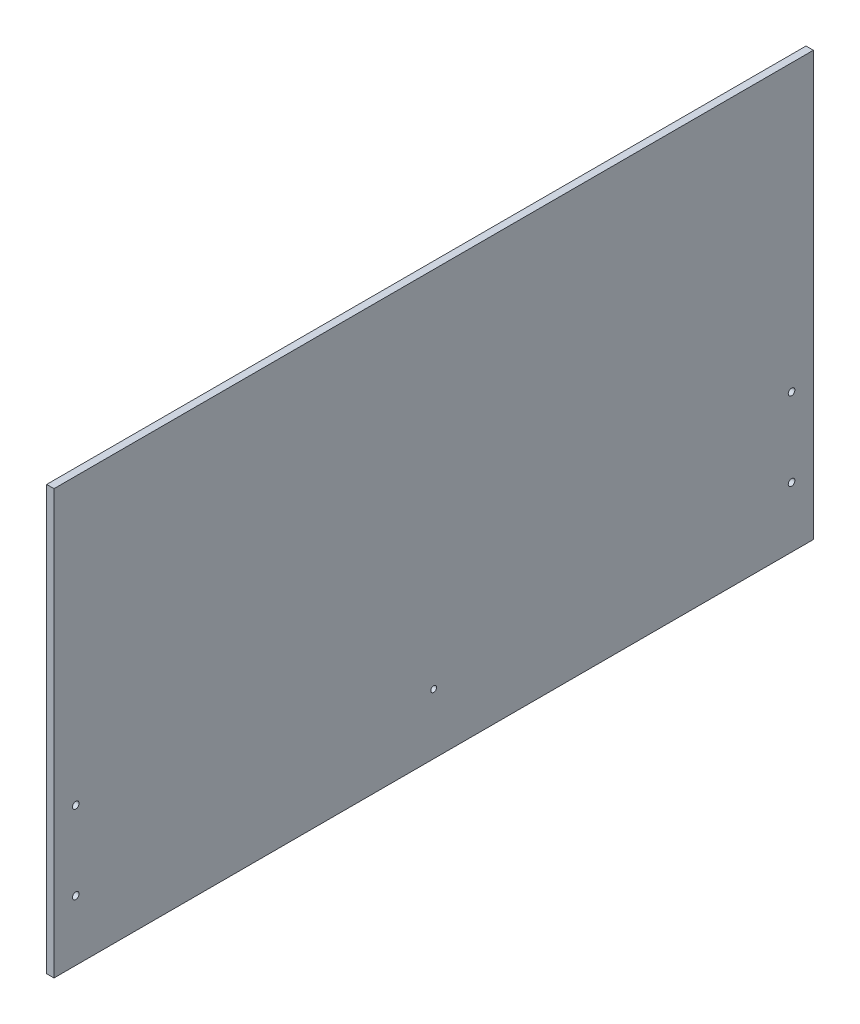
SolidWorks part; units mm, degrees
ref_plane "Front Plane" through (0, 0, 0) normal (0, 0, 1) x (1, 0, 0)
ref_plane "Top Plane" through (0, 0, 0) normal (0, 1, 0) x (1, 0, 0)
ref_plane "Right Plane" through (0, 0, 0) normal (1, 0, 0) x (0, 0, -1)
sketch "Sketch1" plane through (0, 0, 0) normal (1, 0, 0) x (0, 0, -1)
  line L1 (-246.0625, -137.3187) -> (246.0625, -137.3187)
  line L2 (-246.0625, -137.3187) -> (-246.0625, 137.3188)
  line L3 (-246.0625, 137.3188) -> (246.0625, 137.3188)
  line L4 (246.0625, -137.3187) -> (246.0625, 137.3188)
  line L5 (-246.0625, -137.3187) -> (246.0625, 137.3188) construction
  line L6 (-246.0625, 137.3188) -> (246.0625, -137.3187) construction
  point P0 (0, 0)
  dimension "D1" = 274.6375
  dimension "D2" = 492.125
extrude "Boss-Extrude1" add sketch "Sketch1" along normal blind 4.7625
sketch "Sketch2" plane through (4.7625, 0, 0) normal (1, 0, 0) x (0, 0, -1)
  line L0 (0, 0) -> (42.4264, 42.4264) construction
  line L1 (-24.8528, -60) -> (24.8528, -60)
  line L2 (-60, -24.8528) -> (-60, 24.8528)
  line L3 (-24.8528, 60) -> (24.8528, 60)
  line L4 (60, -24.8528) -> (60, 24.8528)
  line L5 (-42.4264, -42.4264) -> (42.4264, 42.4264) construction
  line L6 (0, 0) -> (-42.4264, 42.4264) construction
  line L7 (-42.4264, 42.4264) -> (-24.8528, 60) construction
  line L8 (0, 0) -> (42.4264, -42.4264) construction
  line L9 (-42.4264, 42.4264) -> (-60, 24.8528) construction
  line L10 (42.4264, -42.4264) -> (24.8528, -60) construction
  line L11 (42.4264, -42.4264) -> (60, -24.8528) construction
  line L12 (0, 0) -> (0, 60) construction
  line L13 (0, 0) -> (0, -60) construction
  line L14 (42.4264, 42.4264) -> (60, 24.8528) construction
  line L15 (42.4264, 42.4264) -> (24.8528, 60) construction
  line L16 (-42.4264, -42.4264) -> (-24.8528, -60) construction
  line L17 (-42.4264, -42.4264) -> (-60, -24.8528) construction
  line L18 (-24.8528, 60) -> (-60, 24.8528)
  line L19 (24.8528, 60) -> (60, 24.8528)
  line L20 (42.4264, -42.4264) -> (60, -24.8528)
  line L21 (24.8528, -60) -> (42.4264, -42.4264)
  line L22 (-60, -24.8528) -> (-24.8528, -60)
  point P0 (0, 0)
  dimension "D2" = 60
extrude "Cut-Extrude1" cut sketch "Sketch2" against normal up to next
sketch "Sketch3" plane through (0, 0, 246.0625) normal (0, 0, 1) x (1, 0, 0)
  line L1 (0, 137.3188) -> (4.7625, 137.3188)
  line L2 (0, 137.3188) -> (0, -137.3187)
  line L3 (0, -137.3187) -> (4.7625, -137.3187)
  line L4 (4.7625, 137.3188) -> (4.7625, -137.3187)
extrude "Boss-Extrude2" add sketch "Sketch3" against normal up to next
hole_wizard "#8 Clearance Hole1" positions "Sketch5" profile "Sketch4" hole size "#8" standard "ANSI Inch"
sketch "Sketch5" plane through (4.7625, 0, 0) normal (1, 0, 0) x (0, 0, -1)
  line L1 (-246.0625, 137.3188) -> (-246.0625, -137.3187) construction
  line L2 (-246.0625, -137.3187) -> (246.0625, -137.3187) construction
  line L3 (246.0625, -137.3187) -> (246.0625, 137.3188) construction
  point P0 (-231.9338, -98.2027)
  point P2 (-231.9338, -47.4027)
  point P4 (231.9337, -47.4027)
  point P6 (231.9337, -98.2027)
  dimension "D1" = 14.1287
  dimension "D2" = 89.916
  dimension "D3" = 39.116
  dimension "D4" = 14.1288
sketch "Sketch4" plane through (4.7625, -98.2027, 231.9338) normal (0, 1, 0) x (0, 0, -1)
  line L0 (0, 0) -> (0, 75.7154)
  line L1 (0, 75.7154) -> (2.1526, 74.422)
  line L2 (2.1526, 74.422) -> (2.1526, 0)
  line L5 (2.1526, 0) -> (0, 0)
  line L10 (0, 75.7154) -> (-2.1527, 74.422) construction
  line L11 (0, -6.35) -> (0, 107.95) construction
  dimension "Hole Dia." = 4.3053
  dimension "Hole Depth" = 74.422
  dimension "Drill Angle" = 118
hole_wizard "#6 Clearance Hole1" positions "Sketch7" profile "Sketch6" hole size "#6" standard "ANSI Inch"
sketch "Sketch7" plane through (4.7625, 0, 0) normal (1, 0, 0) x (0, 0, -1)
  line L0 (-231.9338, -98.2027) -> (231.9337, -98.2027) construction
  point P0 (0, -98.2027)
  point P11 (0, -98.2027)
sketch "Sketch6" plane through (4.7625, -98.2027, 0) normal (0, 1, 0) x (0, 0, -1)
  line L0 (0, 0) -> (0, 26.5408)
  line L1 (0, 26.5408) -> (1.8986, 25.4)
  line L2 (1.8986, 25.4) -> (1.8986, 0)
  line L5 (1.8986, 0) -> (0, 0)
  line L10 (0, 26.5408) -> (-1.8987, 25.4) construction
  line L11 (0, -6.35) -> (0, 107.95) construction
  dimension "Hole Dia." = 3.7973
  dimension "Hole Depth" = 25.4
  dimension "Drill Angle" = 118
